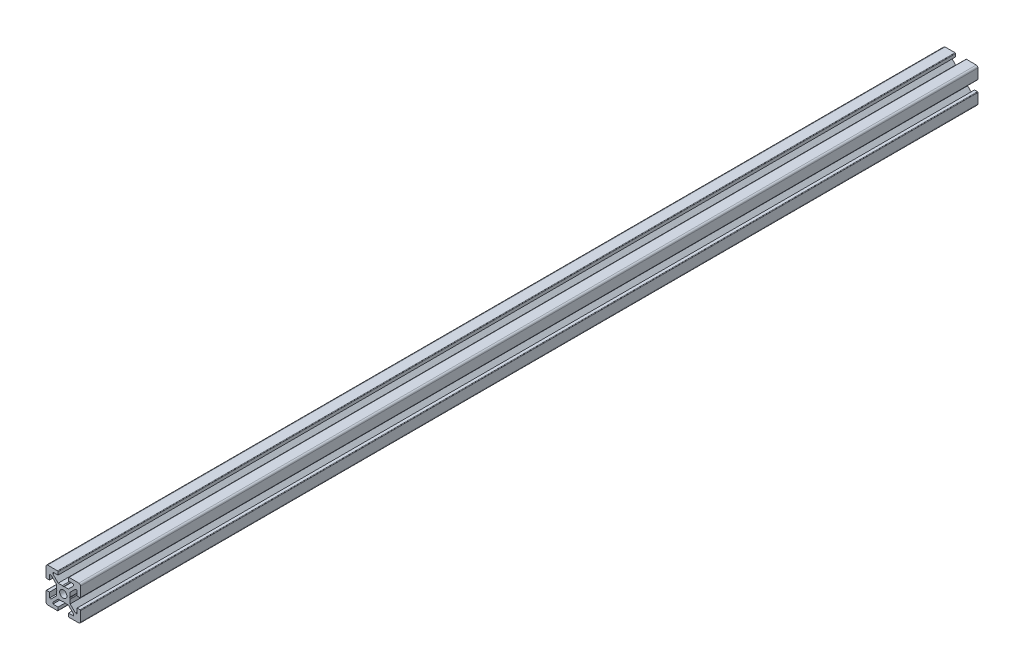
SolidWorks part; units mm, degrees
ref_plane "Front Plane" through (0, 0, 0) normal (0, 0, 1) x (1, 0, 0)
ref_plane "Top Plane" through (0, 0, 0) normal (0, 1, 0) x (1, 0, 0)
ref_plane "Right Plane" through (0, 0, 0) normal (1, 0, 0) x (0, 0, -1)
ref_plane "Plane1" through (0, 0, 0) normal (0, 0, 1) x (1, 0, 0)
sketch "Sketch1" plane through (0, 0, 0) normal (0, 0, 1) x (1, 0, 0)
  line L0 (-10, 9) -> (-10, 3.3)
  line L1 (-9.7, 3) -> (-8, 3)
  line L2 (-8, 3) -> (-8, 6)
  line L3 (-8, 6) -> (-7.0607, 6)
  line L4 (-7.0607, 6) -> (-4, 2.9393)
  line L5 (-4, 2.9393) -> (-4, 0.5196)
  line L6 (-4, 0.5196) -> (-3.7, 0)
  line L7 (-3.7, 0) -> (-4, -0.5196)
  line L8 (-4, -0.5196) -> (-4, -2.9393)
  line L9 (-4, -2.9393) -> (-7.0607, -6)
  line L10 (-7.0607, -6) -> (-8, -6)
  line L11 (-8, -6) -> (-8, -3)
  line L12 (-8, -3) -> (-9.7, -3)
  line L13 (-10, -3.3) -> (-10, -9)
  line L14 (-9, -10) -> (-3.3, -10)
  line L15 (-3, -9.7) -> (-3, -8)
  line L16 (-3, -8) -> (-6, -8)
  line L17 (-6, -8) -> (-6, -7.0607)
  line L18 (-6, -7.0607) -> (-2.9393, -4)
  line L19 (-2.9393, -4) -> (-0.5196, -4)
  line L20 (-0.5196, -4) -> (0, -3.7)
  line L21 (0, -3.7) -> (0.5196, -4)
  line L22 (0.5196, -4) -> (2.9393, -4)
  line L23 (2.9393, -4) -> (6, -7.0607)
  line L24 (6, -7.0607) -> (6, -8)
  line L25 (6, -8) -> (3, -8)
  line L26 (3, -8) -> (3, -9.7)
  line L27 (3.3, -10) -> (9, -10)
  line L28 (10, -9) -> (10, -3.3)
  line L29 (9.7, -3) -> (8, -3)
  line L30 (8, -3) -> (8, -6)
  line L31 (8, -6) -> (7.0606, -6)
  line L32 (7.0606, -6) -> (4, -2.9393)
  line L33 (4, -2.9393) -> (4, -0.5196)
  line L34 (4, -0.5196) -> (3.7, 0)
  line L35 (3.7, 0) -> (4, 0.5196)
  line L36 (4, 0.5196) -> (4, 2.9393)
  line L37 (4, 2.9393) -> (7.0607, 6)
  line L38 (7.0607, 6) -> (8, 6)
  line L39 (8, 6) -> (8, 3)
  line L40 (8, 3) -> (9.7, 3)
  line L41 (10, 3.3) -> (10, 9)
  line L42 (9, 10) -> (3.3, 10)
  line L43 (3, 9.7) -> (3, 8)
  line L44 (3, 8) -> (6, 8)
  line L45 (6, 8) -> (6, 7.0607)
  line L46 (6, 7.0607) -> (2.9393, 4)
  line L47 (2.9393, 4) -> (0.5196, 4)
  line L48 (0.5196, 4) -> (0, 3.7)
  line L49 (0, 3.7) -> (-0.5196, 4)
  line L50 (-0.5196, 4) -> (-2.9394, 4)
  line L51 (-2.9394, 4) -> (-6, 7.0606)
  line L52 (-6, 7.0606) -> (-6, 8)
  line L53 (-6, 8) -> (-3, 8)
  line L54 (-3, 8) -> (-3, 9.7)
  line L55 (-3.3, 10) -> (-9, 10)
  arc A0 (-10, 3.3) -> (-9.7, 3) centre (-9.7, 3.3) ccw
  arc A1 (-9.7, -3) -> (-10, -3.3) centre (-9.7, -3.3) ccw
  arc A2 (-10, -9) -> (-9, -10) centre (-9, -9) ccw
  arc A3 (-3.3, -10) -> (-3, -9.7) centre (-3.3, -9.7) ccw
  arc A4 (3, -9.7) -> (3.3, -10) centre (3.3, -9.7) ccw
  arc A5 (9, -10) -> (10, -9) centre (9, -9) ccw
  arc A6 (10, -3.3) -> (9.7, -3) centre (9.7, -3.3) ccw
  arc A7 (9.7, 3) -> (10, 3.3) centre (9.7, 3.3) ccw
  arc A8 (10, 9) -> (9, 10) centre (9, 9) ccw
  arc A9 (3.3, 10) -> (3, 9.7) centre (3.3, 9.7) ccw
  arc A10 (-3, 9.7) -> (-3.3, 10) centre (-3.3, 9.7) ccw
  arc A11 (-9, 10) -> (-10, 9) centre (-9, 9) ccw
extrude "Boss-Extrude1" add sketch "Sketch1" against normal blind 519.5
ref_plane "Plane2" through (0, 0, 0) normal (1, 0, 0) x (0, 0, -1)
sketch "Sketch2" plane through (0, 0, 0) normal (1, 0, 0) x (0, 0, -1)
  line L0 (0, 0) -> (0, 2.1)
  line L1 (0, 2.1) -> (519.5, 2.1)
  line L2 (519.5, 2.1) -> (519.5, 0)
  line L3 (519.5, 0) -> (0, 0)
  line L4 (519.5, 0) -> (0, 0) construction
revolve "Cut-Revolve1" cut sketch "Sketch2" angle 360 about L4
sketch "Sketch4" plane through (0, 10, 0) normal (0, -1, 0) x (0, 0, -1)
  line L2 (519.5, 0) -> (0, 0) construction
  circle A0 centre (59.75, 0) radius 2.6
  circle A1 centre (459.75, 0) radius 2.6
  circle A2 centre (259.75, 0) radius 2.6
  dimension "D1" = 5.2
  dimension "D2" = 400
  dimension "D3" = 200
extrude "Cut-Extrude2" cut sketch "Sketch4" along normal up to surface (20 mm away) contours A1 | A0 up to face at (6.15, -10, -259.75)
equation "\"D3@Sketch4\"=\"D2@Sketch4\"/2"
